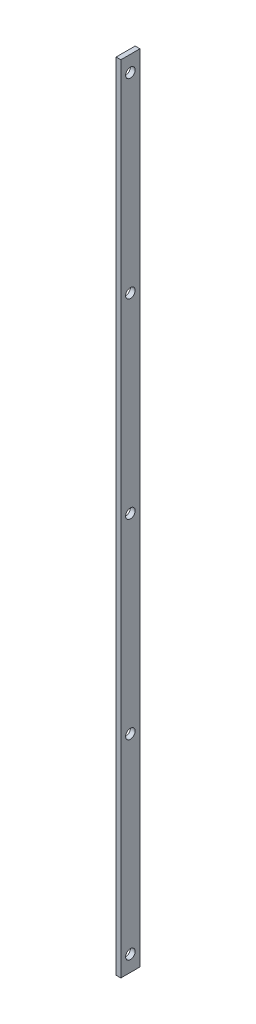
SolidWorks part; units mm, degrees
ref_plane "Front Plane" through (0, 0, 0) normal (0, 0, 1) x (1, 0, 0)
ref_plane "Top Plane" through (0, 0, 0) normal (0, 1, 0) x (1, 0, 0)
ref_plane "Right Plane" through (0, 0, 0) normal (1, 0, 0) x (0, 0, -1)
sketch "Sketch1" plane through (0, 0, 0) normal (1, 0, 0) x (0, 0, -1)
  line L1 (-6, -250) -> (6, -250)
  line L2 (-6, -250) -> (-6, 250)
  line L3 (-6, 250) -> (6, 250)
  line L4 (6, -250) -> (6, 250)
  line L5 (-6, -250) -> (6, 250) construction
  line L6 (-6, 250) -> (6, -250) construction
  point P0 (0, 0)
  dimension "D1" = 500
  dimension "D2" = 12
extrude "Boss-Extrude1" add sketch "Sketch1" along normal blind 3
sketch "Sketch3" plane through (0, 0, 0) normal (-1, 0, 0) x (0, 0, 1)
  line L0 (-6, 250) -> (6, 250) construction
  circle A0 centre (0, 240) radius 3
  circle A1 centre (0, 120) radius 3
  circle A2 centre (0, 0) radius 3
  circle A3 centre (0, -120) radius 3
  circle A4 centre (0, -240) radius 3
  dimension "D1" = 10
  dimension "D2" = 5
extrude "Cut-Extrude1" cut sketch "Sketch3" against normal up to surface (3 mm away) up to face at (3, 0, 0)
